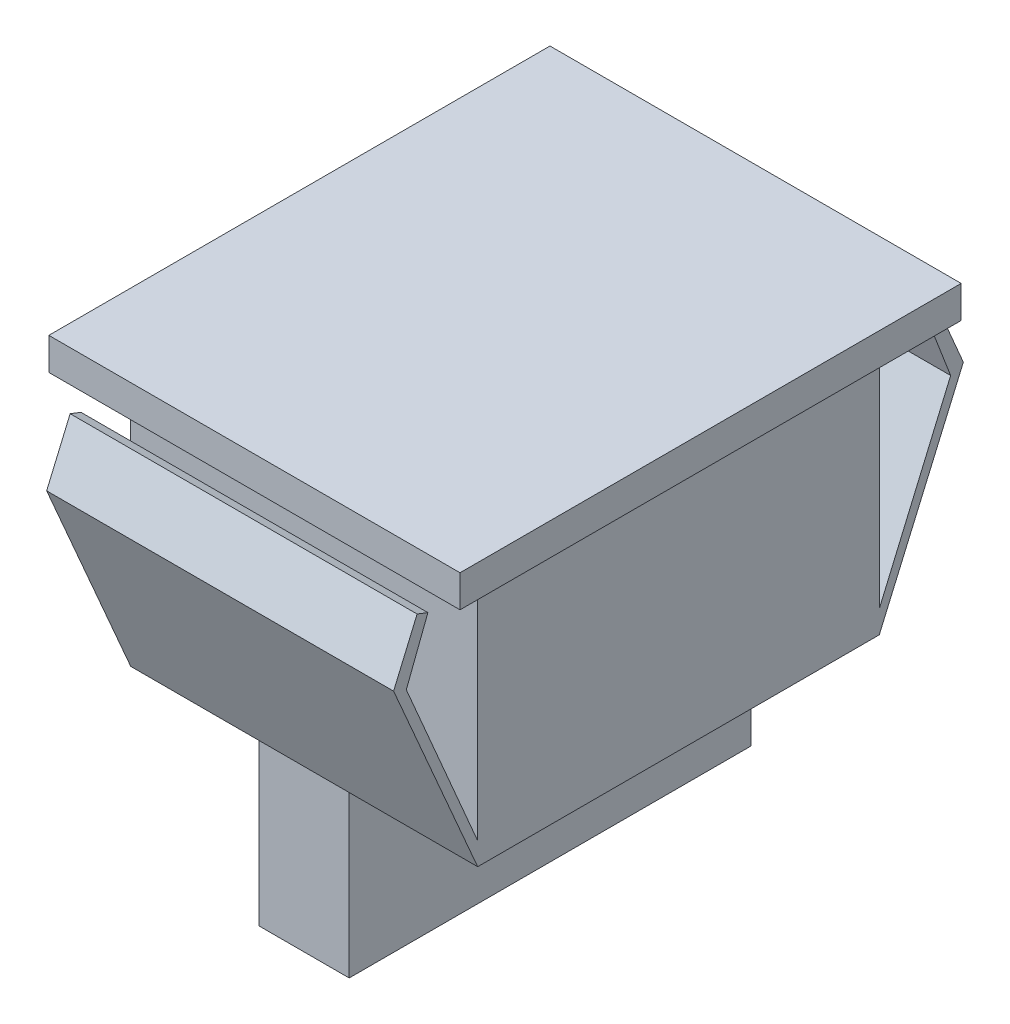
SolidWorks part; units mm, degrees
ref_plane "Спереди" through (0, 0, 0) normal (0, 0, 1) x (1, 0, 0)
ref_plane "Сверху" through (0, 0, 0) normal (0, 1, 0) x (1, 0, 0)
ref_plane "Справа" through (0, 0, 0) normal (1, 0, 0) x (0, 0, -1)
sketch "Эскиз1" plane through (0, 0, 0) normal (1, 0, 0) x (0, 0, -1)
  line L0 (12.5, 0) -> (-12.5, 0)
  line L1 (-12.5, 0) -> (-12.5, 10)
  line L2 (-12.5, 10) -> (-17.7359, 22.0856)
  line L3 (-17.7359, 22.0856) -> (-16.2722, 25.5105)
  line L4 (-16.2722, 25.5105) -> (-15.6, 25.2515)
  line L5 (-15.6, 25.2515) -> (-16.9444, 21.7619)
  line L6 (-16.9444, 21.7619) -> (-12.5, 11.4009)
  line L7 (-12.5, 11.4009) -> (-12.5, 24.7092)
  line L8 (-12.5, 24.7092) -> (-13.75, 24.7092)
  line L9 (-13.75, 24.7092) -> (-13.75, 26.4)
  line L10 (-13.75, 26.4) -> (-15.6, 26.4)
  line L11 (-15.6, 26.4) -> (-15.6, 28.4)
  line L12 (-15.6, 28.4) -> (15.6, 28.4)
  line L13 (0, 41.1034) -> (0, -10.0177) construction
  line L14 (15.6, 26.4) -> (15.6, 28.4)
  line L15 (13.75, 26.4) -> (15.6, 26.4)
  line L16 (13.75, 24.7092) -> (13.75, 26.4)
  line L17 (12.5, 24.7092) -> (13.75, 24.7092)
  line L18 (12.5, 11.4009) -> (12.5, 24.7092)
  line L19 (16.9444, 21.7619) -> (12.5, 11.4009)
  line L20 (15.6, 25.2515) -> (16.9444, 21.7619)
  line L21 (16.2722, 25.5105) -> (15.6, 25.2515)
  line L22 (17.7359, 22.0856) -> (16.2722, 25.5105)
  line L23 (12.5, 10) -> (17.7359, 22.0856)
  line L24 (12.5, 0) -> (12.5, 10)
  point P18 (0, 28.4)
  point P29 (0, 0)
extrude "Бобышка-Вытянуть1" add sketch "Эскиз1" along normal blind 25.6
sketch "Эскиз2" plane through (0, 0, 12.5) normal (0, 0, 1) x (1, 0, 0)
  line L0 (12.8, 0) -> (12.8, 31.8794) construction
  line L1 (25.6, 0) -> (0, 0) construction
  line L3 (2, 10) -> (2, 26.4)
  line L4 (25.6, 26.4) -> (0, 26.4) construction
  line L5 (2, 26.4) -> (0, 26.4)
  line L6 (0, 26.4) -> (0, 28.4)
  line L7 (0, 28.4) -> (0, 26.4) construction
  line L9 (25.6, 28.4) -> (0, 28.4) construction
  line L13 (0, 28.4) -> (25.6, 28.4)
  line L14 (2, 10) -> (10, 10)
  line L15 (25.6, 10) -> (0, 10) construction
  line L16 (10, 10) -> (10, 0)
  line L17 (10, 0) -> (15.6, 0)
  line L18 (15.6, 10) -> (15.6, 0)
  line L19 (23.6, 10) -> (15.6, 10)
  line L20 (25.6, 26.4) -> (25.6, 28.4)
  line L21 (23.6, 26.4) -> (25.6, 26.4)
  line L22 (23.6, 10) -> (23.6, 26.4)
  point P4 (0, 0)
  point P21 (12.8, 28.4)
  point P26 (12.8, 28.4)
extrude "Вырез-Вытянуть1" cut sketch "Эскиз2" against normal through all both and the other way through all flip side to cut
